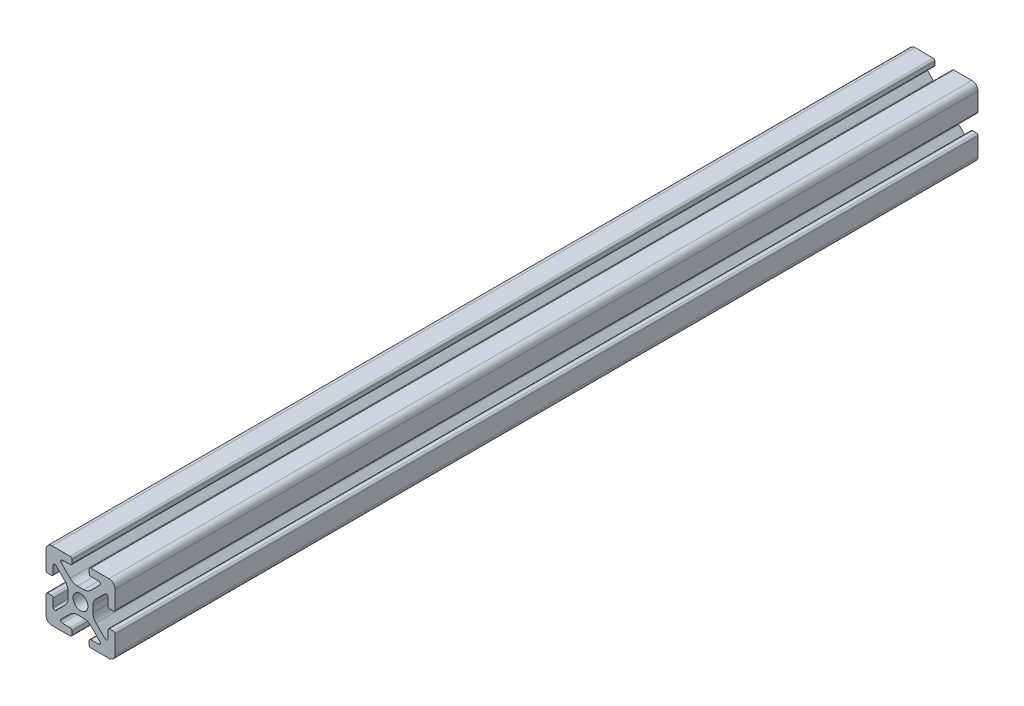
SolidWorks part; units mm, degrees
material "6061 Alloy"
ref_plane "Front Plane" through (0, 0, 0) normal (0, 0, 1) x (1, 0, 0)
ref_plane "Top Plane" through (0, 0, 0) normal (0, 1, 0) x (1, 0, 0)
ref_plane "Right Plane" through (0, 0, 0) normal (1, 0, 0) x (0, 0, -1)
sketch "Sketch2" plane through (0, 0, 0) normal (0, 0, 1) x (1, 0, 0)
  line L0 (0, 10) -> (0, -10) construction
  line L1 (-10, 0) -> (10, 0) construction
  line L2 (2.5, -10) -> (10, -10)
  line L3 (10, -10) -> (10, -2.5)
  line L4 (2.5, -10) -> (2.5, -7.9246)
  line L5 (2.5, -7.9246) -> (6.4571, -7.9246)
  line L6 (6.4571, -7.9246) -> (2.1325, -3.6)
  line L7 (0, 0) -> (10, -10) construction
  line L8 (10, -2.5) -> (7.9246, -2.5)
  line L9 (7.9246, -2.5) -> (7.9246, -6.4571)
  line L10 (7.9246, -6.4571) -> (3.6, -2.1325)
  line L11 (5.7623, -4.2948) -> (4.2948, -5.7623) construction
  circle A0 centre (0, 0) radius 2.15
  arc A1 (5.25, -7.9246) -> (5.6036, -7.0711) centre (5.25, -7.4246) ccw construction
  point P8 (0, -3.6)
  point P16 (5.0286, -5.0286)
  dimension "Center Hole Diameter" = 4.3
  dimension "D3" = 0.5
  dimension "Rail Height" = 20
  dimension "Rail Width" = 20
  dimension "T-Slot Width" = 5
  dimension "Slot Depth" = 6.4
  dimension "Slot Inner Width" = 11.5
sketch "Sketch3" plane through (0, 0, 0) normal (1, 0, 0) x (0, 0, -1)
  line L0 (-152.4, -10) -> (152.4, -10) construction
  line L1 (-127, 0) -> (127, 0) construction
  line L2 (0, 10) -> (0, -10) construction
  line L3 (0, 10) -> (0, -10) construction
  point P6 (-127, 0)
  point P8 (127, 0)
  dimension "Length" = 304.8
  dimension "D1" = 25.4
sketch "Sketch4" plane through (0, 0, 0) normal (0, 0, 1) x (1, 0, 0)
  line L0 (3, -10) -> (8.25, -10)
  line L1 (2.5, -10) -> (10, -10) construction
  line L2 (2.5, -10) -> (2.5, -7.9246) construction
  line L3 (2.5, -7.9246) -> (6.4571, -7.9246) construction
  line L4 (2.5, -8.4246) -> (2.5, -9.5)
  line L5 (3, -7.9246) -> (5.25, -7.9246)
  line L6 (0, -3.6) -> (0.8898, -3.6)
  line L7 (6.4571, -7.9246) -> (2.1325, -3.6) construction
  line L8 (3.0112, -4.4787) -> (5.6036, -7.0711)
  line L9 (10, -10) -> (10, -2.5) construction
  line L10 (7.9246, -6.4571) -> (3.6, -2.1325) construction
  line L11 (7.9246, -2.5) -> (7.9246, -6.4571) construction
  line L12 (7.9246, -5.25) -> (7.9246, -3)
  line L13 (10, -2.5) -> (7.9246, -2.5) construction
  line L14 (8.4246, -2.5) -> (9.5, -2.5)
  line L15 (10, -3) -> (10, -8.25)
  line L16 (7.0711, -5.6036) -> (4.4787, -3.0112)
  line L17 (3.6, 0) -> (3.6, -0.8898)
  line L18 (-10, 0) -> (10, 0) construction
  line L19 (0, -3.6) -> (0, -2.15)
  line L20 (0, 10) -> (0, -10) construction
  line L21 (3.6, 0) -> (2.15, 0)
  arc A0 (2.5, -9.5) -> (3, -10) centre (3, -9.5) ccw
  arc A1 (5.25, -7.9246) -> (5.6036, -7.0711) centre (5.25, -7.4246) ccw construction
  arc A2 (2.5, -8.4246) -> (3, -7.9246) centre (3, -8.4246) cw
  arc A3 (5.25, -7.9246) -> (5.6036, -7.0711) centre (5.25, -7.4246) ccw
  arc A4 (0.8898, -3.6) -> (3.0112, -4.4787) centre (0.8898, -6.6) cw
  arc A5 (8.25, -10) -> (10, -8.25) centre (8.25, -8.25) ccw
  arc A6 (7.0711, -5.6036) -> (7.9246, -5.25) centre (7.4246, -5.25) ccw
  arc A7 (7.9246, -3) -> (8.4246, -2.5) centre (8.4246, -3) cw
  arc A8 (9.5, -2.5) -> (10, -3) centre (9.5, -3) cw
  arc A9 (4.4787, -3.0112) -> (3.6, -0.8898) centre (6.6, -0.8898) cw
  circle A10 centre (0, 0) radius 2.15 construction
  arc A11 (0, -2.15) -> (2.15, 0) centre (0, 0) ccw
  dimension "D1" = 1.75
  dimension "D2" = 3
extrude "Boss-Extrude1" add sketch "Sketch4" along normal mid plane 250
mirror "Mirror1" about plane through (0, 0, 0) normal (1, 0, 0) of bodies 134
mirror "Mirror2" about plane through (0, 0, 0) normal (0, 1, 0) of bodies 135
equation "\"D3@Sketch2\"=\"T-Slot Width@Sketch2\"*0.1"
equation "\"D1@Sketch4\"=\"D3@Sketch2\"*3.5"
equation "\"D2@Sketch4\"=\"D3@Sketch2\"*6"
equation "\"D1@Boss-Extrude1\"=\"Length@Sketch3\""
